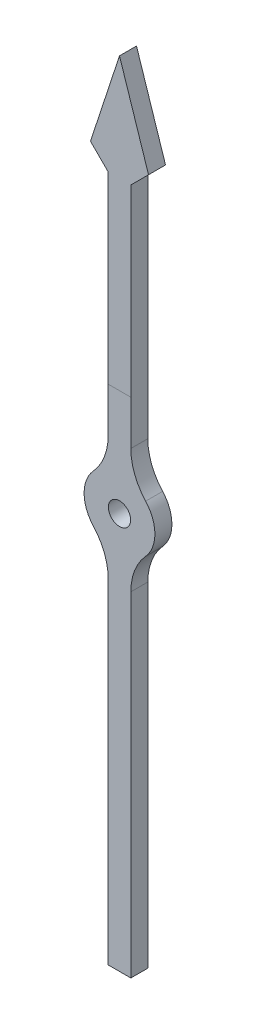
SolidWorks part; units mm, degrees
material "Acrylic (Medium-high impact)"
ref_plane "Front Plane" through (0, 0, 0) normal (0, 0, 1) x (1, 0, 0)
ref_plane "Top Plane" through (0, 0, 0) normal (0, 1, 0) x (1, 0, 0)
ref_plane "Right Plane" through (0, 0, 0) normal (1, 0, 0) x (0, 0, -1)
sketch "Sketch1" plane through (0, 0, 0) normal (0, 0, 1) x (1, 0, 0)
  line L0 (0, 0) -> (0, 17.78) construction
  line L1 (0, 0) -> (0, -17.78) construction
  line L2 (-0.508, 13.0175) -> (-1.3017, 13.8112)
  line L3 (-0.508, -1.504) -> (-0.508, -17.78)
  line L4 (0.508, -1.504) -> (0.508, -17.78)
  line L5 (-0.508, 0) -> (-0.508, -17.78) construction
  line L6 (0.508, 0) -> (0.508, -17.78) construction
  line L7 (0.508, 1.504) -> (0.508, 13.0175)
  line L8 (-0.508, 1.504) -> (-0.508, 13.0175)
  line L9 (-0.508, 0) -> (-0.508, 17.78) construction
  line L10 (0.508, 0) -> (0.508, 17.78) construction
  line L11 (-1.3017, 13.8112) -> (0, 17.78)
  line L12 (-0.508, -17.78) -> (0.508, -17.78)
  line L13 (1.3017, 13.8112) -> (0, 17.78)
  line L14 (0.508, 13.0175) -> (1.3017, 13.8112)
  circle A0 centre (0, 0) radius 0.5
  arc A1 (0.508, -1.504) -> (0.508, 1.504) centre (0, 0) ccw
  arc A3 (-0.508, 1.504) -> (-0.508, -1.504) centre (0, 0) ccw
  dimension "D1" = 1
  dimension "D2" = 3.175
  dimension "D5" = 0.508
  dimension "D3" = 17.78
  dimension "D4" = 17.78
  dimension "D9" = 4.7625
  dimension "D7" = 0.7937
  dimension "D10" = 3.9688
  dimension "D6" = 0.508
  dimension "D8" = 0.508
extrude "Boss-Extrude1" add sketch "Sketch1" along normal blind 0.762
sketch "Sketch2" plane through (0, 0, 0.762) normal (0, 0, 1) x (1, 0, 0)
  line L0 (-0.508, 4.7752) -> (0.508, 4.7752)
  line L1 (-0.508, 13.0175) -> (-0.508, 1.504) construction
  line L2 (0.508, 1.504) -> (0.508, 13.0175) construction
  dimension "D1" = 4.7752
split line "Split Line1"
fillet "Fillet1" radius 2.54 4 edges at (-0.508, -1.504, 0.381) (0.508, -1.504, 0.381) (0.508, 1.504, 0.381) (-0.508, 1.504, 0.381)
